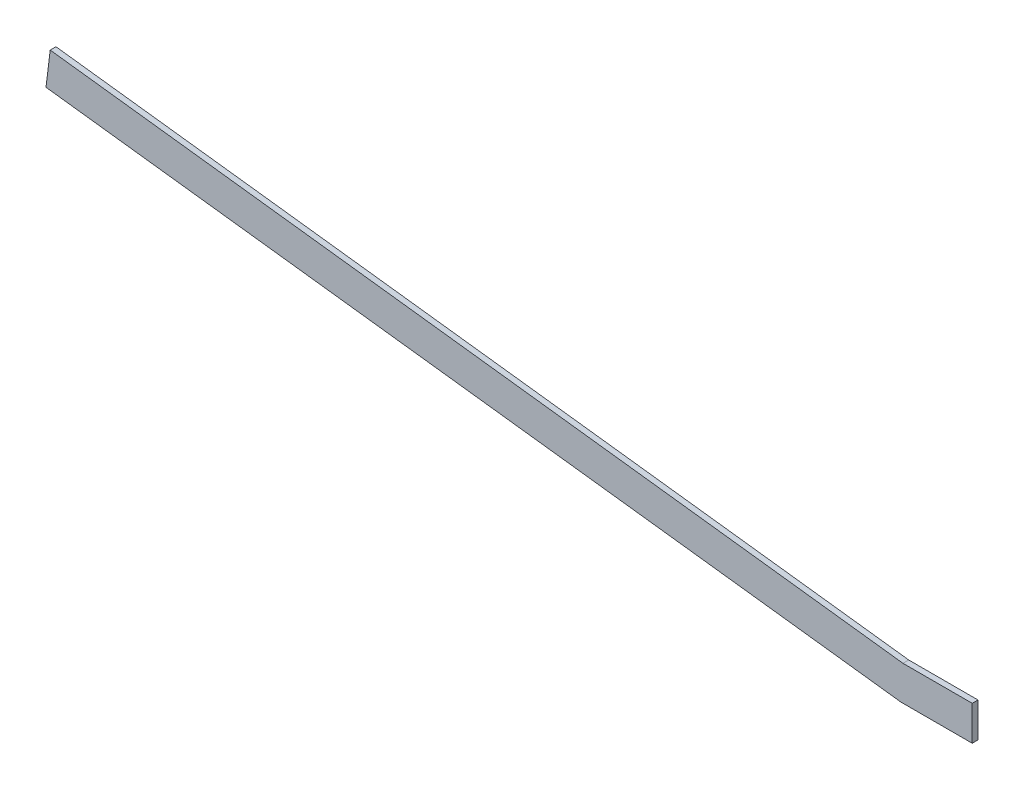
SolidWorks part; units mm, degrees
ref_plane "Front Plane" through (0, 0, 0) normal (0, 0, 1) x (1, 0, 0)
ref_plane "Top Plane" through (0, 0, 0) normal (0, 1, 0) x (1, 0, 0)
ref_plane "Right Plane" through (0, 0, 0) normal (1, 0, 0) x (0, 0, -1)
sketch "Sketch1" plane through (0, 0, 0) normal (0, 0, 1) x (1, 0, 0)
  line L0 (0, 0) -> (-941.0091, 115.5414)
  line L1 (-941.0091, 115.5414) -> (-936.3659, 153.3574)
  line L2 (-936.3659, 153.3574) -> (2.3303, 38.1)
  line L3 (2.3303, 38.1) -> (78.5303, 38.1)
  line L4 (78.5303, 38.1) -> (78.5303, 0)
  line L5 (78.5303, 0) -> (0, 0)
  dimension "D1" = 948.0759
  dimension "D2" = 38.1
  dimension "D3" = 38.1
  dimension "D4" = 76.2
  dimension "D6" = 7
extrude "Boss-Extrude1" add sketch "Sketch1" along normal mid plane 6.35
